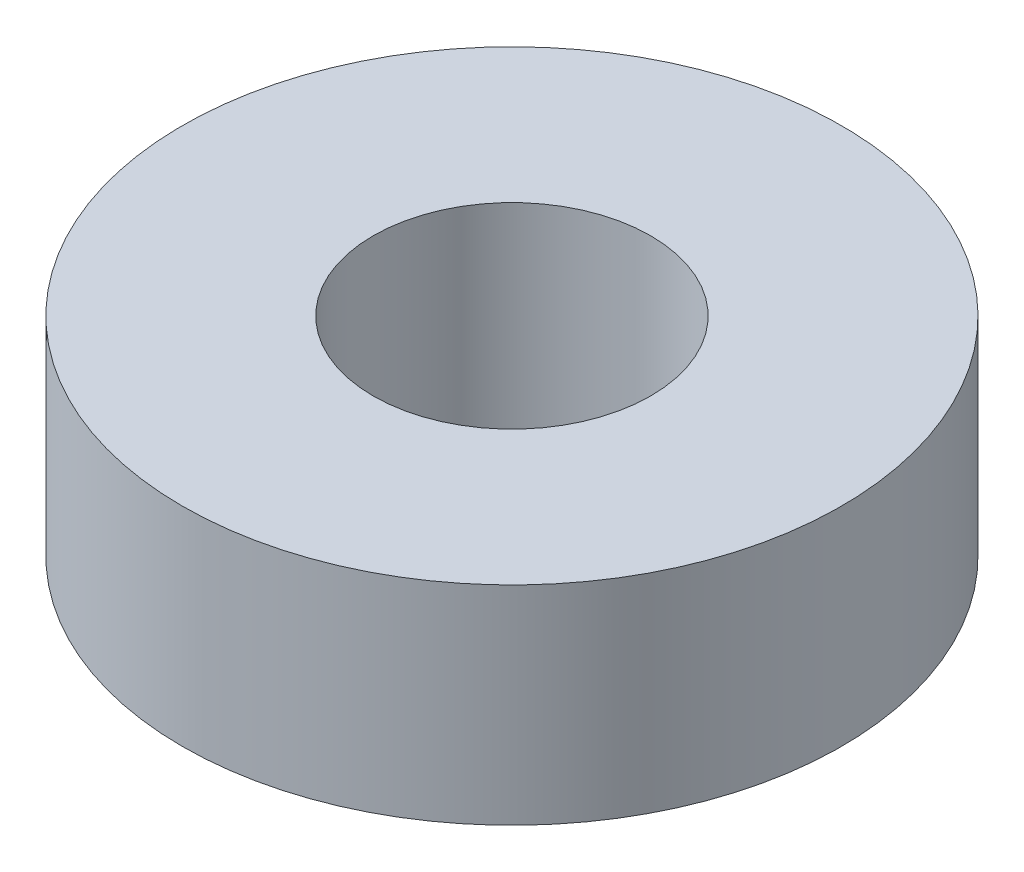
SolidWorks part; units mm, degrees
ref_plane "前视基准面" through (0, 0, 0) normal (0, 0, 1) x (1, 0, 0)
ref_plane "上视基准面" through (0, 0, 0) normal (0, 1, 0) x (1, 0, 0)
ref_plane "右视基准面" through (0, 0, 0) normal (1, 0, 0) x (0, 0, -1)
sketch "Sketch1" plane through (0, 0, 0) normal (0, 1, 0) x (1, 0, 0)
  circle A0 centre (0, 0) radius 4
  circle A1 centre (0, 0) radius 9.5
  dimension "D1" = 8
  dimension "D2" = 19
extrude "Boss-Extrude1" add sketch "Sketch1" along normal blind 6
